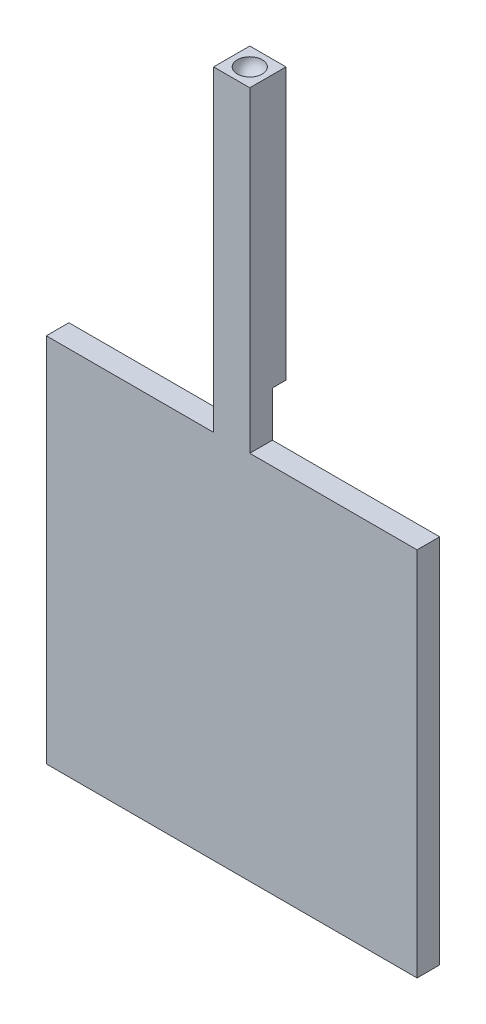
SolidWorks part; units mm, degrees
ref_plane "Front Plane" through (0, 0, 0) normal (0, 0, 1) x (1, 0, 0)
ref_plane "Top Plane" through (0, 0, 0) normal (0, 1, 0) x (1, 0, 0)
ref_plane "Right Plane" through (0, 0, 0) normal (1, 0, 0) x (0, 0, -1)
sketch "Sketch1" plane through (0, 0, 0) normal (0, 0, 1) x (1, 0, 0)
  line L1 (0, 0) -> (82, 0)
  line L2 (0, 0) -> (0, 82)
  line L3 (0, 82) -> (82, 82)
  line L4 (82, 0) -> (82, 82)
  dimension "D1" = 82
  dimension "D2" = 82
extrude "Boss-Extrude1" add sketch "Sketch1" along normal blind 5
sketch "Sketch2" plane through (0, 82, 0) normal (0, 1, 0) x (1, 0, 0)
  line L0 (41, 0) -> (41, -5) construction
  line L1 (82, 0) -> (0, 0) construction
  line L2 (82, -5) -> (0, -5) construction
  line L4 (37, 0) -> (45, 0)
  line L5 (37, 0) -> (37, -5)
  line L6 (37, -5) -> (45, -5)
  line L7 (45, 0) -> (45, -5)
  line L8 (37, 0) -> (45, -5) construction
  line L9 (37, -5) -> (45, 0) construction
  point P6 (41, -2.5)
  dimension "D1" = 8
extrude "Boss-Extrude2" add sketch "Sketch2" along normal blind 10
sketch "Sketch4" plane through (0, 92, 0) normal (0, 1, 0) x (1, 0, 0)
  line L0 (41, -1) -> (41, -5) construction
  line L1 (37, -5) -> (45, -5) construction
  line L3 (45, 3) -> (37, 3)
  line L4 (45, 3) -> (45, -5)
  line L5 (45, -5) -> (37, -5)
  line L6 (37, 3) -> (37, -5)
  line L7 (45, 3) -> (37, -5) construction
  line L8 (45, -5) -> (37, 3) construction
  point P8 (0, 0)
  dimension "D1" = 8
  dimension "D2" = 8
extrude "Boss-Extrude4" add sketch "Sketch4" along normal blind 60
sketch "Sketch5" plane through (0, 152, 0) normal (0, 1, 0) x (1, 0, 0)
  line L0 (38.25, -1) -> (43.75, -1)
  line L3 (41, -1) -> (41, 3) construction
  line L4 (45, 3) -> (37, 3) construction
  arc A1 (43.75, -1) -> (38.25, -1) centre (41, -1) cw
revolve "Cut-Revolve1" cut sketch "Sketch5" angle 180 about L0
sketch "Sketch6" plane through (0, 0, 0) normal (0, 0, -1) x (-1, 0, 0)
  line L3 (-37.5, 15) -> (-44.5, 15)
  line L4 (-37.5, 15) -> (-37.5, 40)
  line L5 (-37.5, 40) -> (-44.5, 40)
  line L6 (-44.5, 15) -> (-44.5, 40)
  dimension "D1" = 7
  dimension "D2" = 25
revolve "Revolve1" add sketch "Sketch6" angle 180 about L5
